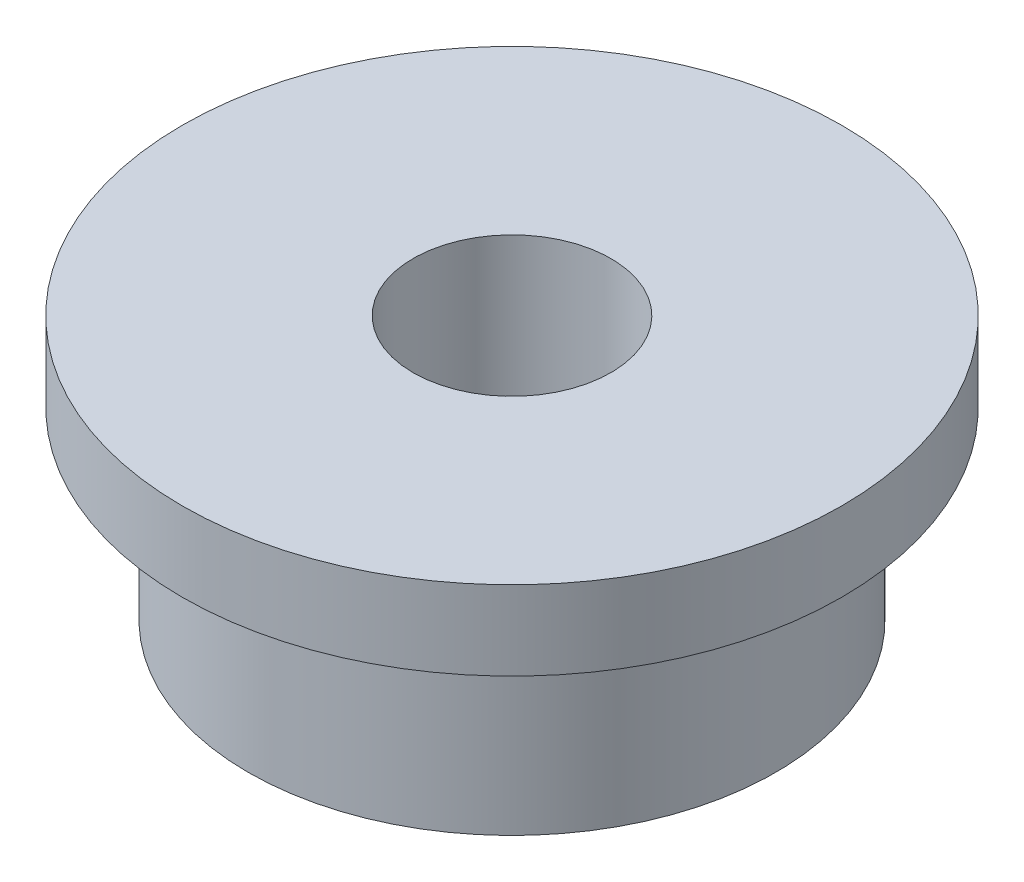
SolidWorks part; units mm, degrees
ref_plane "Front Plane" through (0, 0, 0) normal (0, 0, 1) x (1, 0, 0)
ref_plane "Top Plane" through (0, 0, 0) normal (0, 1, 0) x (1, 0, 0)
ref_plane "Right Plane" through (0, 0, 0) normal (1, 0, 0) x (0, 0, -1)
sketch "Sketch1" plane through (0, 0, 0) normal (0, 1, 0) x (1, 0, 0)
  circle A0 centre (0, 0) radius 0.75
  circle A1 centre (0, 0) radius 2
  dimension "D1" = 1.5
  dimension "D2" = 4
extrude "Boss-Extrude1" add sketch "Sketch1" along normal blind 2
sketch "Sketch2" plane through (0, 2, 0) normal (0, 1, 0) x (1, 0, 0)
  circle A0 centre (0, 0) radius 2
  circle A1 centre (0, 0) radius 2.5
  dimension "D1" = 5
extrude "Boss-Extrude2" add sketch "Sketch2" against normal blind 0.6
